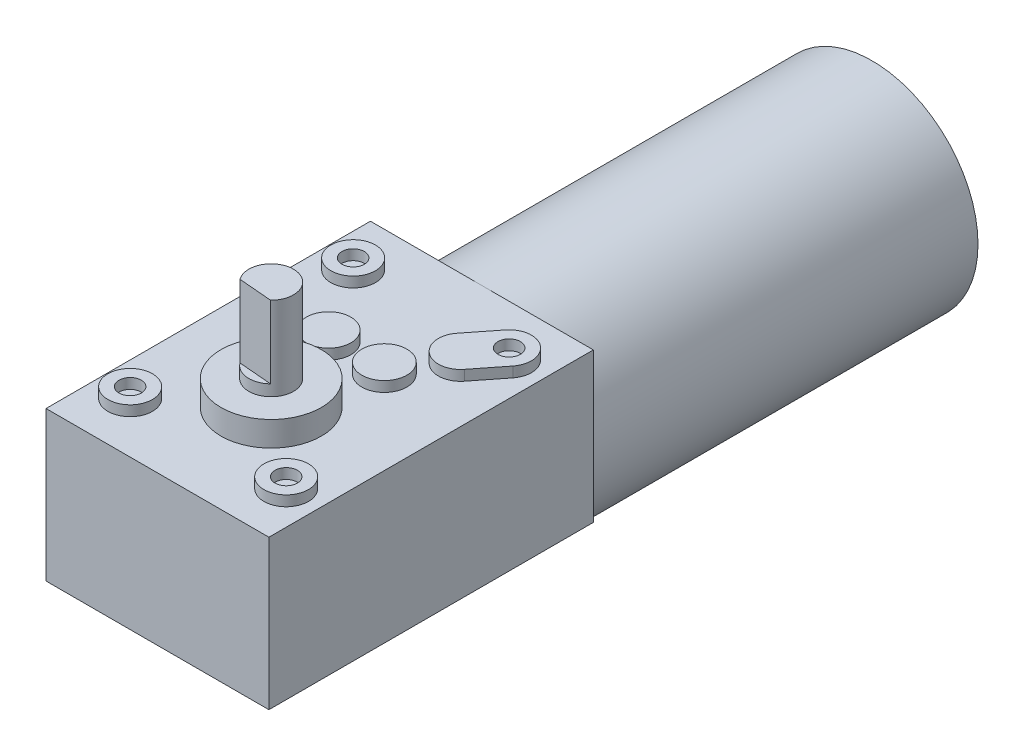
SolidWorks part; units mm, degrees
ref_plane "前视基准面" through (0, 0, 0) normal (0, 0, 1) x (1, 0, 0)
ref_plane "上视基准面" through (0, 0, 0) normal (0, 1, 0) x (1, 0, 0)
ref_plane "右视基准面" through (0, 0, 0) normal (1, 0, 0) x (0, 0, -1)
sketch "草图1" plane through (0, 0, 0) normal (0, 0, 1) x (1, 0, 0)
  circle A0 centre (0, 0) radius 19
extrude "电机" add sketch "草图1" along normal blind 70
sketch "草图2" plane through (0, 0, 70) normal (0, 0, 1) x (1, 0, 0)
  line L11 (-19.9951, 19.0673) -> (19.9951, 19.0673)
  line L12 (-19.9951, 19.0673) -> (-19.9951, -7.7373)
  line L13 (-19.9951, -7.7373) -> (19.9951, -7.7373)
  line L14 (19.9951, 19.0673) -> (19.9951, -7.7373)
  line L15 (-19.9951, 19.0673) -> (19.9951, -7.7373) construction
  line L16 (-19.9951, -7.7373) -> (19.9951, 19.0673) construction
  point P4 (0, 5.6)
extrude "减速机" add sketch "草图2" along normal blind 58.2
sketch "草图3" plane through (0, 19.0673, 0) normal (0, 1, 0) x (1, 0, 0)
  line L0 (13.9951, -79.1) -> (10.155, -83.9739) construction
  line L1 (17.1309, -81.5706) -> (13.2909, -86.4446)
  line L2 (10.8593, -76.6294) -> (7.0192, -81.5033)
  line L5 (19.9951, -128.2) -> (19.9951, -70) construction
  line L6 (-19.9951, -128.2) -> (-19.9951, -70) construction
  circle A0 centre (13.9951, -119.1) radius 4
  circle A1 centre (-13.9951, -119.1) radius 4
  circle A3 centre (-13.9951, -79.1) radius 4
  circle A5 centre (0, -107.8) radius 9
  circle A7 centre (5, -92.5) radius 4.05
  circle A8 centre (-5, -92.5) radius 4
  circle A9 centre (13.9951, -119.1) radius 2
  circle A10 centre (-13.9951, -119.1) radius 2
  circle A11 centre (13.9951, -79.1) radius 2
  circle A12 centre (-13.9951, -79.1) radius 2
  arc A13 (17.1309, -81.5706) -> (10.8593, -76.6294) centre (13.9951, -79.1) ccw
  arc A14 (7.0192, -81.5033) -> (13.2909, -86.4446) centre (10.155, -83.9739) ccw
  point P8 (12.0751, -81.537)
  point P20 (0, 0)
  dimension "D1" = 8
  dimension "D2" = 4
  dimension "D3" = 6
  dimension "D4" = 6
  dimension "D5" = 6
  dimension "D6" = 6
extrude "减速机外突起" add sketch "草图3" against normal blind 28.65 and the other way blind 1.85 separate body
sketch "草图5" plane through (0, 20.9173, 0) normal (0, 1, 0) x (1, 0, 0)
  circle A0 centre (0, -107.8) radius 9
extrude "减速机抽头盘" add sketch "草图5" along normal blind 2.6 and the other way blind 33.1
sketch "草图6" plane through (0, 23.5173, 0) normal (0, 1, 0) x (1, 0, 0)
  circle A0 centre (0, -107.8) radius 4
extrude "减速机抽头" add sketch "草图6" along normal blind 2
sketch "草图7" plane through (0, 25.5173, 0) normal (0, 1, 0) x (1, 0, 0)
  line L0 (2.7727, -110.6831) -> (-3.2176, -110.1763)
  arc A0 (-3.2176, -110.1763) -> (2.7727, -110.6831) centre (0, -107.8) cw
  circle A1 centre (0, -107.8) radius 4 construction
extrude "D型轴" add sketch "草图7" along normal blind 13
